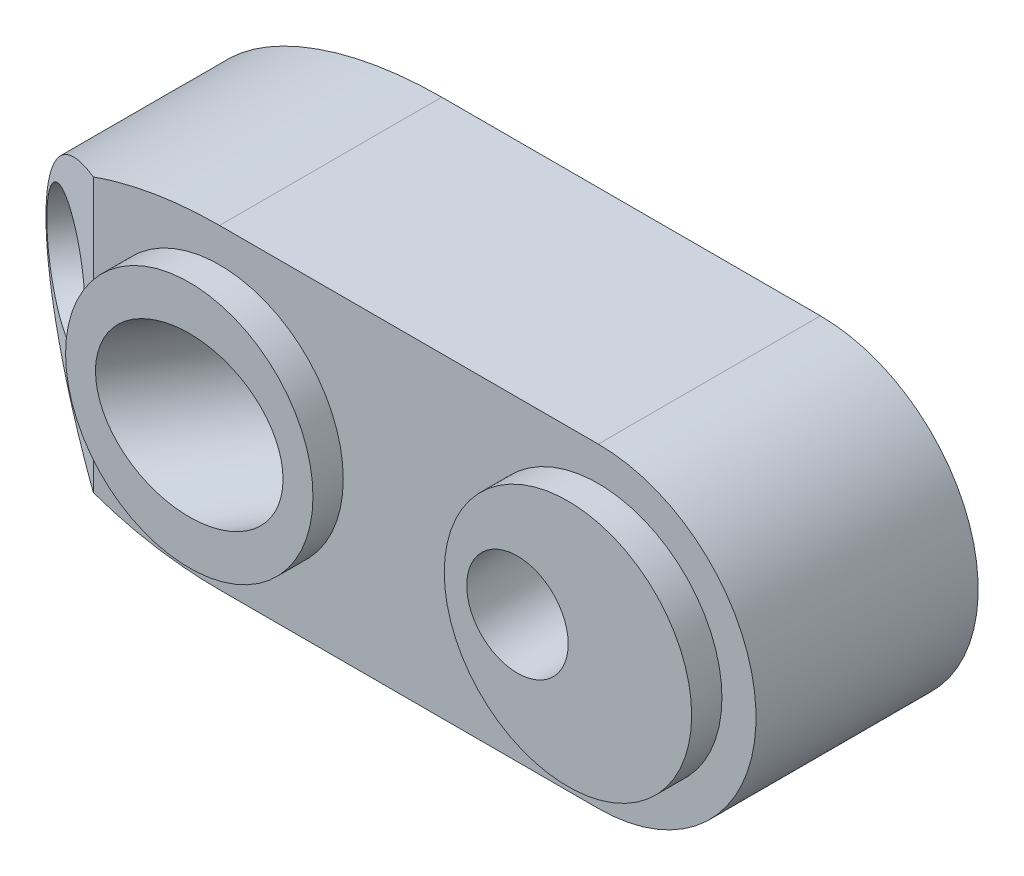
SolidWorks part; units mm, degrees
ref_plane "Front" through (0, 0, 0) normal (0, 0, 1) x (1, 0, 0)
ref_plane "Top" through (0, 0, 0) normal (0, 1, 0) x (1, 0, 0)
ref_plane "Right" through (0, 0, 0) normal (1, 0, 0) x (0, 0, -1)
sketch "Sketch1" plane through (0, 0, 0) normal (0, 0, 1) x (1, 0, 0)
  line L0 (0, 7.9375) -> (19.05, 7.9375)
  line L1 (0, -7.9375) -> (19.05, -7.9375)
  line L2 (0, 0) -> (0, -3.5453) construction
  arc A0 (0, 7.9375) -> (0, -7.9375) centre (0, 0) ccw construction
  arc A1 (19.05, -7.9375) -> (19.05, 7.9375) centre (19.05, 0) ccw
  ellipse E0 centre (0, 0) end of major axis (-12.7, 0) minor radius 7.9375 (0, 7.9375) -> (0, -7.9375) ccw
  dimension "D1" = 19.05
  dimension "D2" = 15.875
  dimension "D3" = 12.7
extrude "Boss-Extrude1" add sketch "Sketch1" against normal blind 12.7
sketch "Sketch2" plane through (0, 0, 0) normal (0, 0, 1) x (1, 0, 0)
  circle A2 centre (0, 0) radius 6.223
  circle A3 centre (19.05, 0) radius 6.223
  dimension "D1" = 12.446
extrude "Cut-Extrude1" cut sketch "Sketch2" against normal blind 1.524 flip side to cut
ref_plane "Plane1" through (0, 0, 0) normal (-0.5299, 0, 0.848) x (0, -1, 0)
sketch "Sketch3" plane through (0, 0, 0) normal (-0.5299, 0, 0.848) x (0, -1, 0)
  line L0 (0, 0) -> (0, -10.5) construction
  circle A0 centre (0, 0) radius 4
  dimension "D1" = 8
  dimension "D2" = 10.5
extrude "Cut-Extrude2" cut sketch "Sketch3" against normal through all both and the other way through all
ref_plane "Plane2" through (3.365, 0, -5.3851) normal (-0.5299, 0, 0.848) x (0, -1, 0)
sketch "Sketch5" plane through (3.365, 0, -5.3851) normal (-0.5299, 0, 0.848) x (0, -1, 0)
  line L0 (5.5, 5.5) -> (0, 0) construction
  line L1 (5.5, 5.5) -> (-5.5, 5.5)
  line L2 (5.5, 5.5) -> (5.5, -15.5)
  line L3 (5.5, -15.5) -> (-5.5, -15.5)
  line L4 (-5.5, 5.5) -> (-5.5, -15.5)
  line L5 (0, 0) -> (-5.5, 5.5) construction
  dimension "D1" = 11
  dimension "D2" = 21
extrude "Cut-Extrude3" cut sketch "Sketch5" against normal through all
sketch "Sketch8" plane through (0, 0, 0) normal (0, 1, 0) x (1, 0, 0)
  line L0 (-12.7, 5.4919) -> (-6.35, 1.524)
  line L1 (-12.7, 5.4919) -> (-14.4832, 2.6382)
  line L2 (-6.35, 1.524) -> (-8.1332, -1.3297)
  line L3 (-14.4832, 2.6382) -> (-8.1332, -1.3297)
  line L9 (-12.7, 1.524) -> (0, 1.524) construction
  line L10 (-12.7, 12.7) -> (-12.7, 1.524) construction
  line L11 (1.7114, 6.4184) -> (5.0186, 4.3518) construction
  line L12 (-12.7, 12.7) -> (-12.7, 1.524) construction
  point P7 (-14.1223, 8.4001)
  dimension "D1" = 6.35
extrude "Cut-Extrude4" cut sketch "Sketch8" against normal through all both and the other way through all
sketch "Sketch4" plane through (0, 0, 0) normal (0, 1, 0) x (1, 0, 0)
  line L0 (-3.8147, 13.7095) -> (-10.0028, 3.8065)
  line L1 (-10.0028, 3.8065) -> (-12.5876, 5.4217)
  line L2 (-12.5876, 5.4217) -> (-10.8164, 8.2564)
  line L3 (-10.8164, 8.2564) -> (-9.847, 7.6507)
  line L4 (-9.847, 7.6507) -> (-5.4303, 14.719)
  line L5 (-5.4303, 14.719) -> (-3.8147, 13.7095)
  line L6 (-3.8147, 13.7095) -> (-2.1992, 12.7) construction
  line L8 (0, 0) -> (-8.9045, 5.5642) construction
  line L9 (-10.0028, 3.8065) -> (-13.5324, -1.8421) construction
  line L10 (-8.3413, 12.7) -> (8.0293, 2.4705) construction
  line L11 (19.05, 12.7) -> (0, 12.7) construction
  dimension "D1" = 3.81
  dimension "D2" = 5.08
  dimension "D3" = 6.096
revolve "Cut-Revolve1" cut sketch "Sketch4" angle 360 about L9
hole_wizard "1/4-20 Tapped Hole1" positions "Sketch6" profile "Sketch7" tap size "1/4-20" standard "ANSI Inch" end condition through all
sketch "Sketch6" plane through (0, 0, 0) normal (0, 0, 1) x (1, 0, 0)
  circle A0 centre (19.05, 0) radius 6.223 construction
  point P0 (16.51, 0)
  dimension "D1" = 2.54
sketch "Sketch7" plane through (16.51, 0, 0) normal (1, 0, 0) x (0, -1, 0)
  line L0 (0, 0) -> (0, 12.7)
  line L1 (0, 12.7) -> (2.5527, 12.7)
  line L2 (2.5527, 12.7) -> (2.5527, 0)
  line L5 (2.5527, 0) -> (0, 0)
  line L11 (0, -6.35) -> (0, 107.95) construction
  dimension "Thru Tap Drill Dia." = 5.1054
  dimension "Thru Tap Drill Depth" = 12.7
cosmetic thread "Hole Thread1" parameters "D2"=6.35
